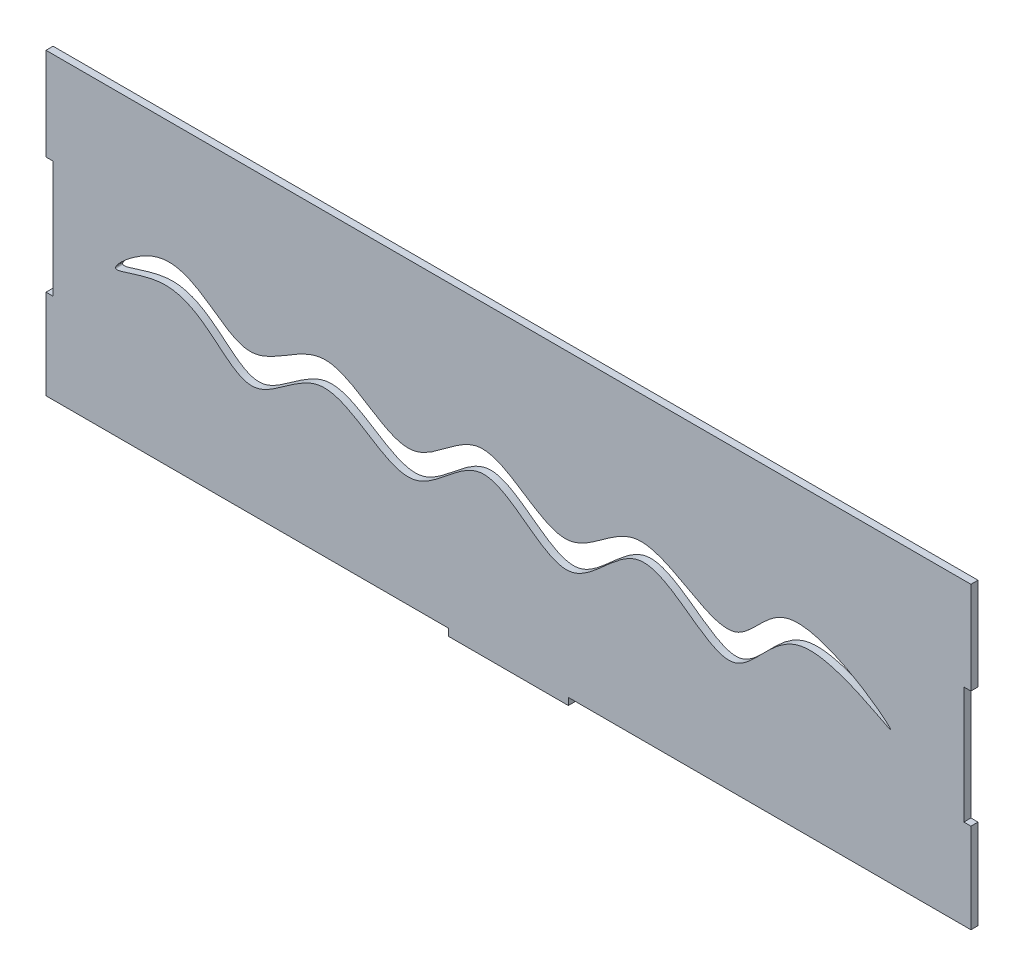
SolidWorks part; units mm, degrees
ref_plane "Front Plane" through (0, 0, 0) normal (0, 0, 1) x (1, 0, 0)
ref_plane "Top Plane" through (0, 0, 0) normal (0, 1, 0) x (1, 0, 0)
ref_plane "Right Plane" through (0, 0, 0) normal (1, 0, 0) x (0, 0, -1)
sketch "Croquis1" plane through (0, 0, 0) normal (0, 0, 1) x (1, 0, 0)
  line L0 (0, 0) -> (148, 0)
  line L1 (340, 0) -> (340, 33)
  line L2 (340, 110) -> (0, 110)
  line L3 (0, 110) -> (0, 76)
  line L4 (170, 110) -> (170, -2.6) construction
  line L6 (148, 0) -> (148, -2.6)
  line L7 (148, -2.6) -> (192, -2.6)
  line L8 (192, 0) -> (192, -2.6)
  line L9 (2.6, 54.5) -> (337.4, 54.5) construction
  line L10 (340, 76) -> (340, 110)
  line L11 (337.4, 76) -> (340, 76)
  line L12 (337.4, 76) -> (337.4, 33)
  line L13 (337.4, 33) -> (340, 33)
  line L15 (0, 76) -> (2.6, 76)
  line L17 (0, 33) -> (2.6, 33)
  line L18 (2.6, 76) -> (2.6, 33)
  line L19 (0, 33) -> (0, 0)
  line L20 (192, 0) -> (340, 0)
  point P22 (337.4, 54.5)
  point P24 (170, -2.6)
  point P26 (2.6, 54.5)
  dimension "D1" = 340
  dimension "D2" = 110
  dimension "D3" = 2.6
  dimension "D4" = 44
  dimension "D5" = 2.6
  dimension "D6" = 2.6
  dimension "D7" = 43
  dimension "D8" = 43
extrude "Saliente-Extruir1" add sketch "Croquis1" along normal blind 2.6
sketch "Croquis2" plane through (0, 0, 2.6) normal (0, 0, 1) x (1, 0, 0)
  spline S0 degree 3 poles (54.6131, 66.4853) (16.8438, 47.3874) (50.1116, 77.489) (71.9215, 37.9868) (103.9973, 75.3027) (133.0711, 36.9978) (160.7892, 76.5579) (190.5143, 36.9472) (218.6004, 76.6495) (252.1862, 38.0506) (272.6553, 80.285) (332.2399, 33.1262) (272.8706, 73.1293) (253.0745, 25.1434) (218.9532, 72.9855) (191.9215, 24.5704) (161.2944, 70.1634) (133.5118, 26.5125) (103.3893, 66.9492) (72.3222, 26.8629) (54.6131, 66.4853) (16.8438, 47.3874) (50.1116, 77.489) knots -0.13082 -0.086938 -0.027807 0 0.029457 0.08786 0.13451 0.18931 0.234303 0.289415 0.334807 0.395128 0.432651 0.49795 0.552147 0.601857 0.659817 0.709438 0.765349 0.812066 0.86918 0.913062 0.972193 1 1.029457 1.08786 1.13451 only from (25.6445, 53.3877) to (25.6445, 53.3877)
  point P2 (75.0777, 51.6498)
  point P4 (133.094, 54.9132)
  point P6 (101.011, 53.6441)
  point P8 (102.3164, 62.7817)
  point P10 (134.6895, 40.8515)
  point P12 (134.4284, 49.9891)
  point P14 (160.2747, 55.4716)
  point P16 (159.4915, 63.3038)
  point P18 (192.1257, 40.3293)
  point P20 (191.6035, 49.9891)
  point P22 (218.7552, 56.777)
  point P24 (251.9115, 41.3736)
  point P26 (253.478, 51.5555)
  point P28 (277.7578, 59.1266)
  point P30 (310.392, 48.9448)
extrude "Cortar-Extruir1" cut sketch "Croquis2" against normal blind 10
